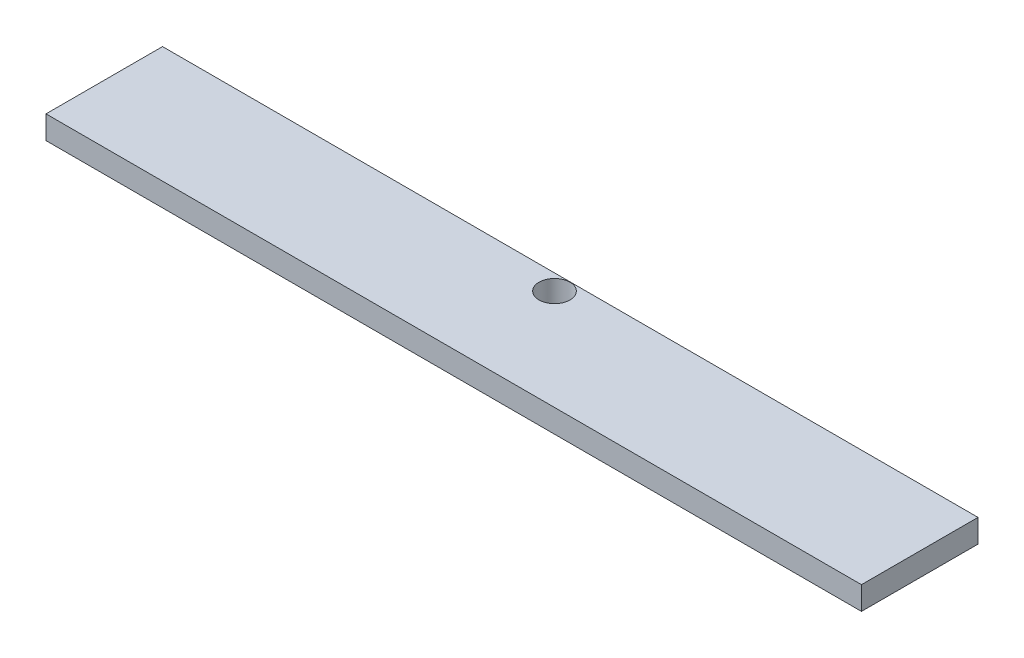
SolidWorks part; units mm, degrees
material "Oak"
ref_plane "Front Plane" through (0, 0, 0) normal (0, 0, 1) x (1, 0, 0)
ref_plane "Top Plane" through (0, 0, 0) normal (0, 1, 0) x (1, 0, 0)
ref_plane "Right Plane" through (0, 0, 0) normal (1, 0, 0) x (0, 0, -1)
sketch "Sketch1" plane through (0, 0, 0) normal (0, 1, 0) x (1, 0, 0)
  line L1 (0, 0) -> (669.925, 0)
  line L2 (0, 0) -> (0, 95.739)
  line L3 (0, 95.739) -> (669.925, 95.739)
  line L4 (669.925, 0) -> (669.925, 95.739)
  dimension "D1" = 95.739
  dimension "D2" = 669.925
extrude "Boss-Extrude1" add sketch "Sketch1" along normal blind 19.05
sketch "Sketch2" plane through (0, 0, 0) normal (0, -1, 0) x (1, 0, 0)
  line L3 (0, -95.739) -> (0, 0) construction
  line L6 (669.925, -95.739) -> (0, -95.739) construction
  circle A0 centre (334.9625, -82.7849) radius 12.7
  dimension "D1" = 25.4
  dimension "D2" = 334.9625
  dimension "D3" = 12.954
extrude "Cut-Extrude4" cut sketch "Sketch2" against normal through all
